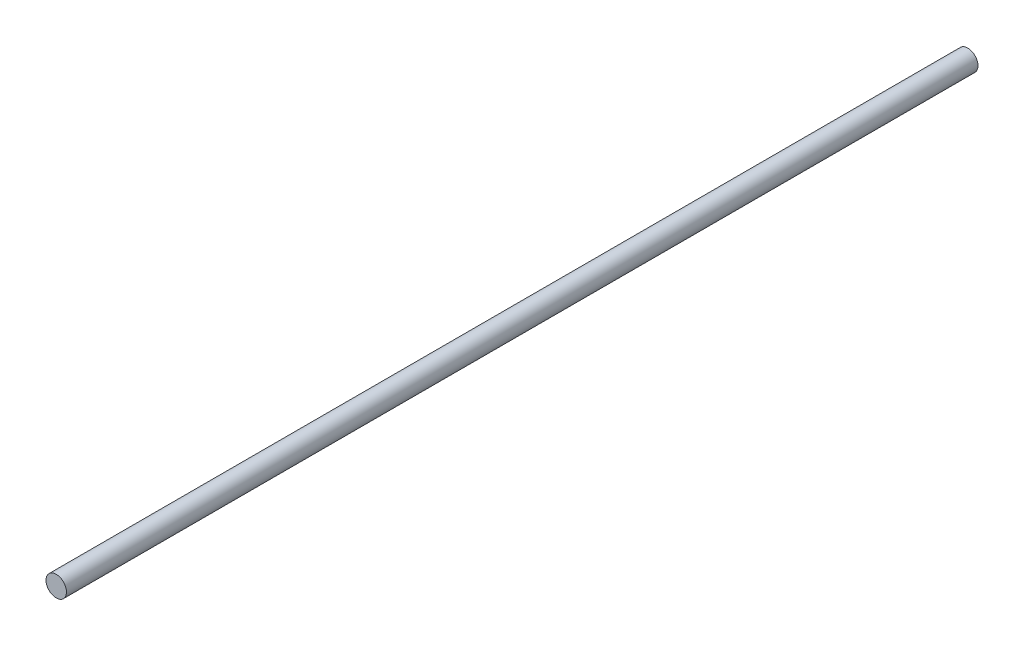
SolidWorks part; units mm, degrees
ref_plane "Alzado" through (0, 0, 0) normal (0, 0, 1) x (1, 0, 0)
ref_plane "Planta" through (0, 0, 0) normal (0, 1, 0) x (1, 0, 0)
ref_plane "Vista lateral" through (0, 0, 0) normal (1, 0, 0) x (0, 0, -1)
sketch "Croquis1" plane through (0, 0, 0) normal (0, 0, 1) x (1, 0, 0)
  circle A0 centre (0, 0) radius 4
  dimension "D1" = 8
extrude "Saliente-Extruir1" add sketch "Croquis1" along normal blind 356
